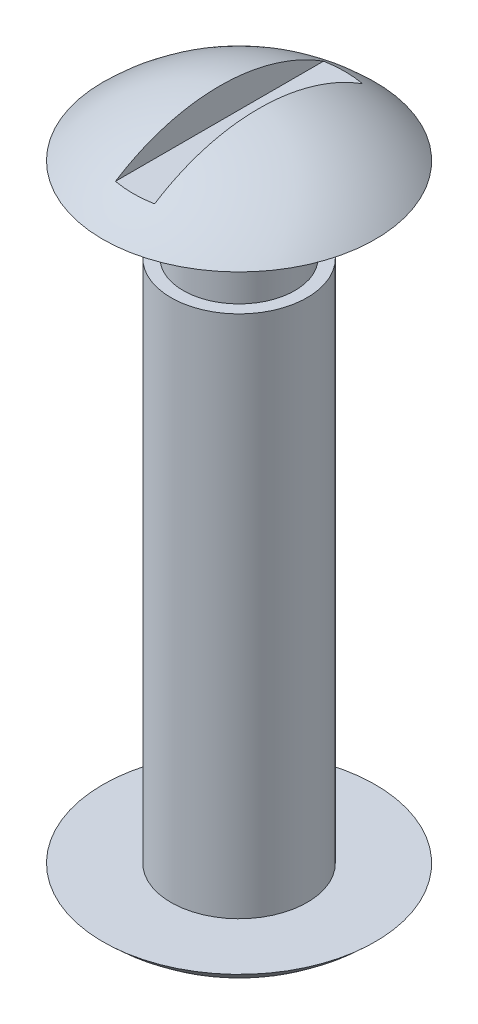
SolidWorks part; units mm, degrees
material "6063-T6"
ref_plane "Front Plane" through (0, 0, 0) normal (0, 0, 1) x (1, 0, 0)
ref_plane "Top Plane" through (0, 0, 0) normal (0, 1, 0) x (1, 0, 0)
ref_plane "Right Plane" through (0, 0, 0) normal (1, 0, 0) x (0, 0, -1)
sketch "Sketch1" plane through (0, 0, 0) normal (0, 0, 1) x (1, 0, 0)
  line L0 (0, 22.1234) -> (0, 0) construction
  line L1 (0, 22.1234) -> (4.953, 22.1234) construction
  line L2 (0, 0) -> (4.953, 0) construction
  line L3 (4.953, 22.1234) -> (2.032, 22.1234)
  line L4 (2.4765, 0) -> (2.4765, 19.05)
  line L5 (2.4765, 0) -> (4.953, 0)
  line L6 (0, 24.1554) -> (0, -2.032)
  line L7 (2.4765, 19.05) -> (2.032, 19.05)
  line L8 (2.032, 19.05) -> (2.032, 22.1234)
  line L9 (4.953, 22.1234) -> (4.953, 19.05) construction
  line L10 (0, -2.032) -> (0, 0) construction
  line L11 (0, 22.1234) -> (0, 24.1554) construction
  line L12 (0, 22.1234) -> (0, 24.1554) construction
  arc A0 (0, 24.1554) -> (4.953, 22.1234) centre (0, 17.1029) cw
  arc A1 (0, -2.032) -> (4.953, 0) centre (0, 5.0205) ccw
  dimension "D1" = 2.4765
  dimension "D2" = 2.032
  dimension "D3" = 19.05
  dimension "D4" = 3.0734
  dimension "D5" = 19.05
  dimension "D6" = 2.032
revolve "Revolve1" add sketch "Sketch1" angle 360 about L6
sketch "Sketch2" plane through (0, 0, 0) normal (0, 0, 1) x (1, 0, 0)
  line L0 (0, 23.0124) -> (0, 0) construction
  line L1 (-0.7112, 24.2824) -> (0.7112, 24.2824)
  line L2 (-0.7112, 24.2824) -> (-0.7112, 23.0124)
  line L3 (-0.7112, 23.0124) -> (0.7112, 23.0124)
  line L4 (0.7112, 24.2824) -> (0.7112, 23.0124)
  line L5 (-2.032, 22.1234) -> (2.032, 22.1234) construction
  dimension "D1" = 1.4224
  dimension "D2" = 0.889
  dimension "D3" = 1.27
extrude "Cut-Extrude1" cut sketch "Sketch2" against normal through all both and the other way through all
equation "\"Height\"= 32in"
equation "\"Width\"= 23in"
equation "\"Depth\"= 20in"
equation "\"Plexi\"= .121in"
equation "\"MagnetThickness\"= 0.125in"
equation "\"MagnetDiameter\"= 12mm"
equation "\"DoorPlexi\"= \"Plexi\""
equation "\"BasePlateThickness\"= 0.5in"
equation "\"BasePlateWidth\"= \"Width\"+\"EBWidth\"-2*\"Plexi\""
equation "\"BasePlateDepth\"= \"TopBarDepth\"+2*\"CornerCube\""
equation "\"Boxsize\"= .75in"
equation "\"Boxinner\"= .625in"
equation "\"CornerCube\"= 0.75in"
equation "\"FingerLength\"= 1.125in"
equation "\"FingerWidth\"= .625in"
equation "\"Cutwidth\"= .016in"
equation "\"Earsize\"= 1in + \"Cutwidth\" /2"
equation "\"Slotsize\"= 1in - \"Cutwidth\" / 2"
equation "\"InnerWidth\"= \"Width\" - 2* \"Plexi\""
equation "\"InnerHeight\"= \"Height\" -2 * \"Plexi\""
equation "\"InnerDepth\"= \"Depth\" - 2*\"Plexi\""
equation "\"RearNumHoles\"= 4"
equation "\"RearHolesBorder\"= 2.25"
equation "\"RearHoleSpacing\"= (\"Width\" - 2*\"RearHolesBorder\") / (\"RearNumHoles\"-1)"
equation "\"RearBarLength\"= (\"InnerWidth\"-2*\"CornerCube\")"
equation "\"RearTopNumHoles\"= 4"
equation "\"RearTopHolesBorder\"= 3.1"
equation "\"RearTopHolesSpacing\"= (\"Width\" - 2*\"RearTopHolesBorder\") / (\"RearTopNumHoles\"-1)"
equation "\"SideTopNumHoles\"= 4"
equation "\"SideTopHoleOffset\"=\"CornerCube\"+\"FingerLength\"+\"Plexi\"+.5"
equation "\"SideTopHoleSpacing\"= (\"TopBarDepth\"-2*\"SideTopHoleOffset\") / (\"SideTopNumHoles\"-1)"
equation "\"SideHorizNumHoles\"= 4"
equation "\"SideHorizHoleBorder\"= 1.50"
equation "\"SideHorizHoleSpacing\"= (\"TopBarDepth\"-2*\"SideHorizHoleBorder\") / (\"SideHorizNumHoles\"-1)"
equation "\"SideVertBarLength\"=\"Height\"-\"BasePlateThickness\"-2*\"CornerCube\"-\"Plexi\""
equation "\"SideVertNumHoles\"= 4"
equation "\"SideVertHolesBorder\"= \"CornerCube\"+\"FingerLength\"+1.50"
equation "\"SideVertHoleSpacing\"= (\"InnerHeight\" - 2*\"SideVertHolesBorder\") / (\"SideVertNumHoles\"-1)"
equation "\"RearSideVertNumHoles\"= 4"
equation "\"RearSideVertHolesBorder\"= 2.4"
equation "\"RearSideVertHoleSpacing\"= (\"InnerHeight\" - 2*\"RearSideVertHolesBorder\") / (\"RearSideVertNumHoles\"-1)"
equation "\"RivetDia\"= .228in"
equation "\"SlotDepth\"= \"Plexi\" + 0.75in + .005in"
equation "\"SideSlotWidth\"= \"Plexi\"+.005in"
equation "\"SidePanelVertSpacing\"= (\"Height\"-2*(1.75-\"Plexi\")) / 5"
equation "\"BottomPanelSideHoleSpacing\"= (\"InnerDepth\"-2*(1.75-\"Plexi\")) / 4"
equation "\"FrontDoorGap\"= .1in"
equation "\"TopDepth\"= \"Depth\"-\"DoorPlexi\"-\"FrontDoorGap\""
equation "\"TopBarDepth\"= \"Depth\"-\"DoorPlexi\"-\"Plexi\"-2*\"MagnetThickness\"-2*\"CornerCube\""
equation "\"D4@Sketch1\"=\"Plexi\""
equation "\"D5@Sketch1\"=\"Boxsize\""
